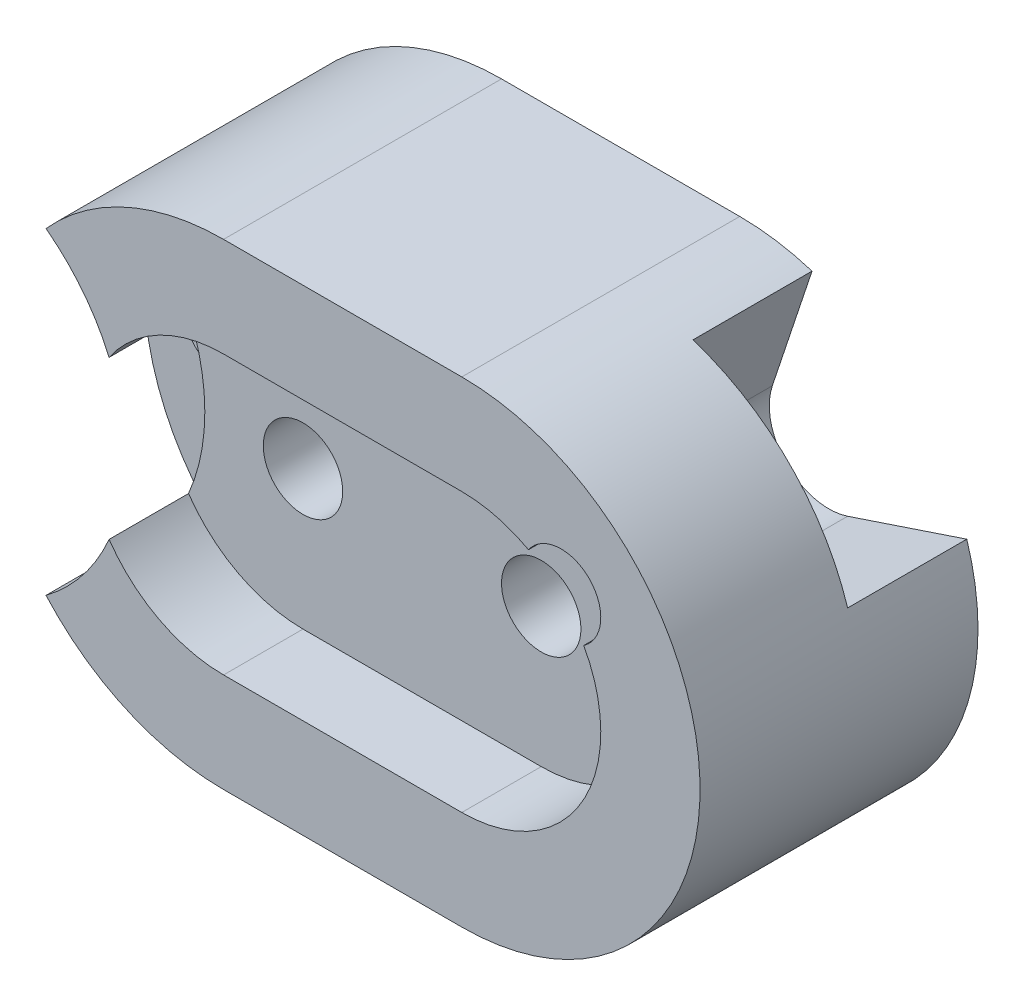
SolidWorks part; units mm, degrees
ref_plane "Front Plane" through (0, 0, 0) normal (0, 0, 1) x (1, 0, 0)
ref_plane "Top Plane" through (0, 0, 0) normal (0, 1, 0) x (1, 0, 0)
ref_plane "Right Plane" through (0, 0, 0) normal (1, 0, 0) x (0, 0, -1)
sketch "Sketch1" plane through (0, 0, 0) normal (0, 0, 1) x (1, 0, 0)
  line L0 (-30, 60) -> (0, 60)
  line L1 (0, 0) -> (-30, 0)
  arc A0 (0, 60) -> (0, 0) centre (0, 30) cw
  arc A1 (-30, 0) -> (-30, 60) centre (-30, 30) cw
  dimension "D2" = 30
  dimension "D1" = 30
extrude "Boss-Extrude1" add sketch "Sketch1" along normal blind 35
sketch "Sketch2" plane through (0, 0, 35) normal (0, 0, 1) x (1, 0, 0)
  line L0 (-30, 30) -> (0, 30) construction
  line L1 (-30, 47.5) -> (0, 47.5)
  line L2 (-30, 12.5) -> (0, 12.5)
  line L3 (0, 60) -> (-30, 60) construction
  arc A0 (-30, 47.5) -> (-30, 12.5) centre (-30, 30) ccw
  arc A1 (0, 12.5) -> (0, 47.5) centre (0, 30) ccw
  point P2 (-15, 30)
  dimension "D1" = 17.5
  dimension "D2" = 12.5
extrude "Cut-Extrude1" cut sketch "Sketch2" against normal blind 10
sketch "Sketch4" plane through (0, 0, 25) normal (0, 0, 1) x (1, 0, 0)
  circle A0 centre (-30, 30) radius 5
  circle A1 centre (0, 30) radius 5
  dimension "D1" = 10
  dimension "D2" = 10
  dimension "D3" = 30
  dimension "D4" = 17.5
extrude "Cut-Extrude2" cut sketch "Sketch4" against normal blind 113
sketch "Sketch5" plane through (0, 0, 35) normal (0, 0, 1) x (1, 0, 0)
  circle A0 centre (12.5, 42.5) radius 5
  dimension "D1" = 12.5
  dimension "D3" = 10
  dimension "D2" = 17.5
extrude "Cut-Extrude3" cut sketch "Sketch5" against normal blind 20
sketch "Sketch6" plane through (0, 0, 35) normal (0, 0, 1) x (1, 0, 0)
  arc A0 (-52.3607, 50) -> (-52.3607, 10) centre (-67.3607, 30) cw
  arc A1 (-30, 60) -> (-30, 0) centre (-30, 30) ccw construction
  arc A2 (-52.3607, 50) -> (-52.3607, 10) centre (-30, 30) ccw
  dimension "D3" = 25
  dimension "D4" = 30
  dimension "D1" = 2.5
  dimension "D2" = 2.5
extrude "Cut-Extrude4" cut sketch "Sketch6" against normal blind 20
sketch "Sketch7" plane through (0, 0, 15) normal (0, 0, 1) x (1, 0, 0)
  circle A0 centre (-50, 30) radius 5
  arc A1 (-44.4145, 20.0767) -> (-44.4145, 39.9233) centre (-67.3607, 30) ccw construction
  arc A2 (-52.3607, 50) -> (-52.3607, 10) centre (-30, 30) ccw construction
  dimension "D1" = 10
  dimension "D2" = 30
  dimension "D3" = 50
extrude "Cut-Extrude5" cut sketch "Sketch7" against normal blind 48
sketch "Sketch8" plane through (0, 0, 0) normal (0, 0, -1) x (-1, 0, 0)
  line L0 (-4.0998, 43.5866) -> (-9.0998, 58.5866)
  line L1 (-13.5866, 34.0998) -> (-28.5866, 39.0998)
  arc A0 (-28.5866, 39.0998) -> (-9.0998, 58.5866) centre (0, 30) cw
  arc A1 (-13.5866, 34.0998) -> (-4.0998, 43.5866) centre (-11.2149, 41.2149) ccw
  arc A2 (0, 60) -> (0, 0) centre (0, 30) ccw construction
  dimension "D3" = 15
  dimension "D5" = 30
  dimension "D2" = 7.5
  dimension "D1" = 5
  dimension "D4" = 5
extrude "Cut-Extrude7" cut sketch "Sketch8" against normal blind 15
